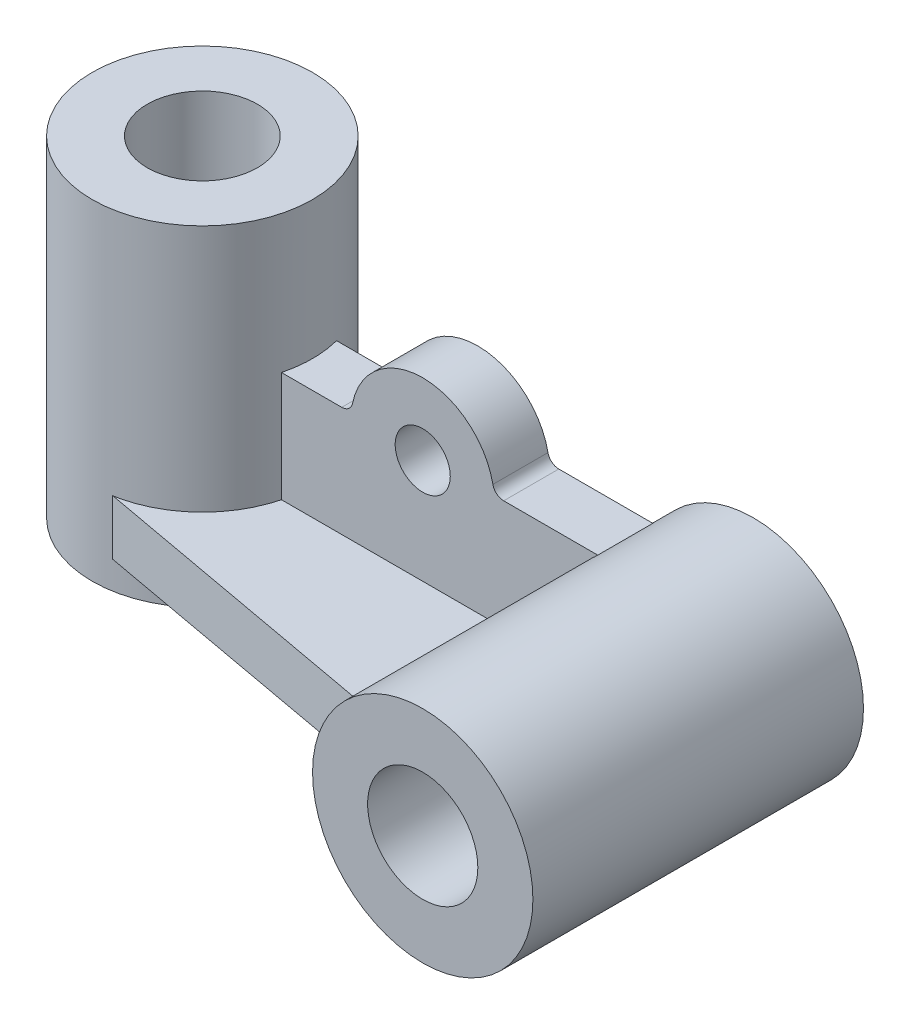
SolidWorks part; units mm, degrees
ref_plane "Front Plane" through (0, 0, 0) normal (0, 0, 1) x (1, 0, 0)
ref_plane "Top Plane" through (0, 0, 0) normal (0, 1, 0) x (1, 0, 0)
ref_plane "Right Plane" through (0, 0, 0) normal (1, 0, 0) x (0, 0, -1)
sketch "Sketch1" plane through (0, 0, 0) normal (0, 0, 1) x (1, 0, 0)
  line L0 (0, 44.4281) -> (0, -80.0714) construction
  line L1 (-28.6057, 0) -> (38.9394, 0) construction
  line L2 (0, 30) -> (0, -30)
  line L3 (0, -30) -> (20, -30)
  line L4 (20, -30) -> (20, 30)
  line L5 (20, 30) -> (0, 30)
  line L6 (10, 30) -> (10, -30)
  dimension "D1" = 60
  dimension "big-cyl-purple" = 20
  dimension "small-cyl-purple" = 10
ref_plane "Plane2" through (0, 0, 50) normal (0, 0, 1) x (1, 0, 0)
sketch "Sketch3" plane through (0, 0, 50) normal (0, 0, 1) x (1, 0, 0)
  line L0 (-41.145, 0) -> (181.0552, 0) construction
  line L1 (0, 53.1866) -> (0, -50.2505) construction
  line L2 (90, 47.9131) -> (90, -59.9766) construction
  line L3 (0, -30) -> (191.1627, -30) construction
  circle A0 centre (90, -10) radius 20
  circle A1 centre (90, -10) radius 10
  dimension "big-cyl-blue" = 40
  dimension "small-cyl-blue" = 20
  dimension "D3" = 90
  dimension "D4" = 30
  dimension "D5" = 20
extrude "cyl- blue" add sketch "Sketch3" against normal blind 60 separate body
ref_plane "Plane3" through (0, 0, -5) normal (0, 0, 1) x (1, 0, 0)
sketch "Sketch4" plane through (0, 0, -5) normal (0, 0, 1) x (1, 0, 0)
  line L0 (-19.6228, -30) -> (145.0037, -30) construction
  line L2 (0, 39.5007) -> (0, -49.1941) construction
  line L4 (-38.69, -15) -> (133.7763, -15) construction
  line L5 (10, -15) -> (70.6351, -15)
  line L6 (10, 5) -> (30.3031, 5)
  line L8 (10, 5) -> (10, -15)
  line L9 (59.6969, 5) -> (76.7712, 5)
  circle A0 centre (90, -10) radius 20 construction
  arc A1 (70.6351, -15) -> (76.7712, 5) centre (90, -10) cw
  circle A4 centre (90, -10) radius 10 construction
  arc A7 (32.2627, 6.6) -> (57.7373, 6.6) centre (45, 4) cw
  circle A8 centre (45, 4) radius 5
  arc A9 (59.6969, 5) -> (57.7373, 6.6) centre (59.6969, 7) cw
  arc A10 (30.3031, 5) -> (32.2627, 6.6) centre (30.3031, 7) ccw
  dimension "D2" = 13
  dimension "D3" = 10
  dimension "D4" = 45
  dimension "D5" = 2
  dimension "D8" = 10
  dimension "D9" = 19
  dimension "D1" = 20
  dimension "D6" = 15
  dimension "D7" = 20
extrude "base- yellow" add sketch "Sketch4" along normal blind 10 separate body
ref_plane "Plane4" through (0, -25, 0) normal (0, 1, 0) x (1, 0, 0)
sketch "Sketch6" plane through (0, -25, 0) normal (0, 1, 0) x (1, 0, 0)
  line L0 (0, 35.6481) -> (0, 20) construction
  line L1 (-44.6641, 0) -> (126.7478, 0) construction
  line L8 (0, 0) -> (0, -43.6764) construction
  line L13 (110, -50) -> (110, -74.8178) construction
  line L17 (10, -5) -> (70.6351, -5) construction
  line L19 (11, -5) -> (76, -5)
  line L21 (60, -30) -> (76, -30)
  line L22 (76, -30) -> (76, -5)
  line L23 (11, -5) -> (-4.3393, -18.2619)
  line L24 (-4.3393, -18.2619) -> (60, -30)
  line L25 (30.3031, -5) -> (10, -5) construction
  point P6 (74, -30)
  point P8 (-8, -18.2619)
  point P19 (-4.3393, -18.2619)
  dimension "D1" = 25
  dimension "D2" = 11
  dimension "D3" = 14
  dimension "D4" = 60
  dimension "D5" = 76
  dimension "D6" = 4.3393
  dimension "D7" = 18.2619
extrude "base-red" add sketch "Sketch6" along normal blind 10 separate body
ref_plane "Plane5" through (0, -30, 0) normal (0, 1, 0) x (1, 0, 0)
sketch "Sketch7" plane through (0, -30, 0) normal (0, 1, 0) x (1, 0, 0)
  line L0 (0, 36.4672) -> (0, -39.8063) construction
  line L1 (-42.417, 0) -> (122.7128, 0) construction
  circle A2 centre (0, 0) radius 20
  circle A3 centre (0, 0) radius 10
  dimension "D1" = 40
  dimension "D2" = 20
extrude "cyl-purple" add sketch "Sketch7" along normal blind 60
equation "\"small-cyl-purple@Sketch1\"=\"big-cyl-purple@Sketch1\"/2"
equation "\"small-cyl-blue@Sketch3\"=\"big-cyl-blue@Sketch3\"/2"
